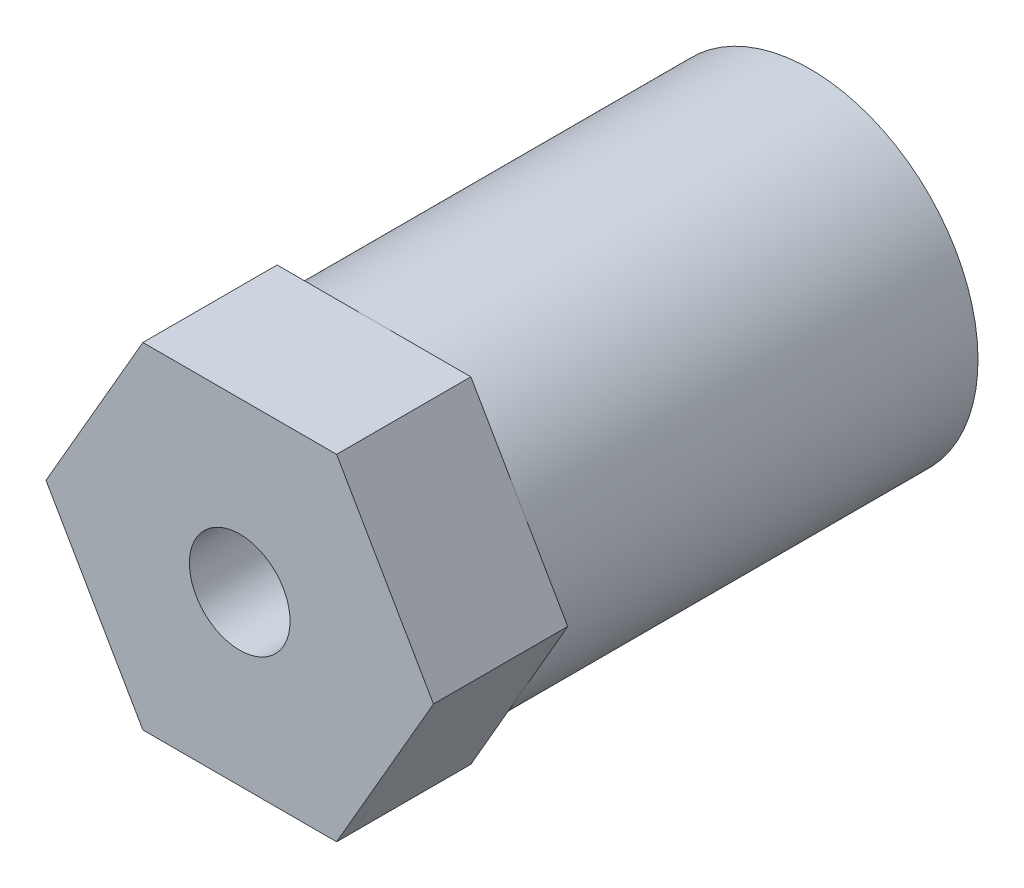
SolidWorks part; units mm, degrees
ref_plane "Alzado" through (0, 0, 0) normal (0, 0, 1) x (1, 0, 0)
ref_plane "Planta" through (0, 0, 0) normal (0, 1, 0) x (1, 0, 0)
ref_plane "Vista lateral" through (0, 0, 0) normal (1, 0, 0) x (0, 0, -1)
sketch "Croquis2" plane through (0, 0, 0) normal (0, 0, 1) x (1, 0, 0)
  line L1 (2.8868, 5) -> (-2.8868, 5)
  line L2 (-2.8868, 5) -> (-5.7735, 0)
  line L3 (-5.7735, 0) -> (-2.8868, -5)
  line L4 (-2.8868, -5) -> (2.8868, -5)
  line L5 (2.8868, -5) -> (5.7735, 0)
  line L6 (5.7735, 0) -> (2.8868, 5)
  circle A0 centre (0, 0) radius 5 construction
  circle A1 centre (0, 0) radius 1.5
  dimension "D1" = 3
  dimension "D2" = 10
extrude "Saliente-Extruir1" add sketch "Croquis2" along normal blind 4
sketch "Croquis3" plane through (0, 0, 0) normal (0, 0, -1) x (-1, 0, 0)
  circle A0 centre (0, 0) radius 5
  circle A1 centre (0, 0) radius 2.5
  dimension "D1" = 10
  dimension "D2" = 5
extrude "Saliente-Extruir2" add sketch "Croquis3" along normal blind 13 contours A0 | A1
